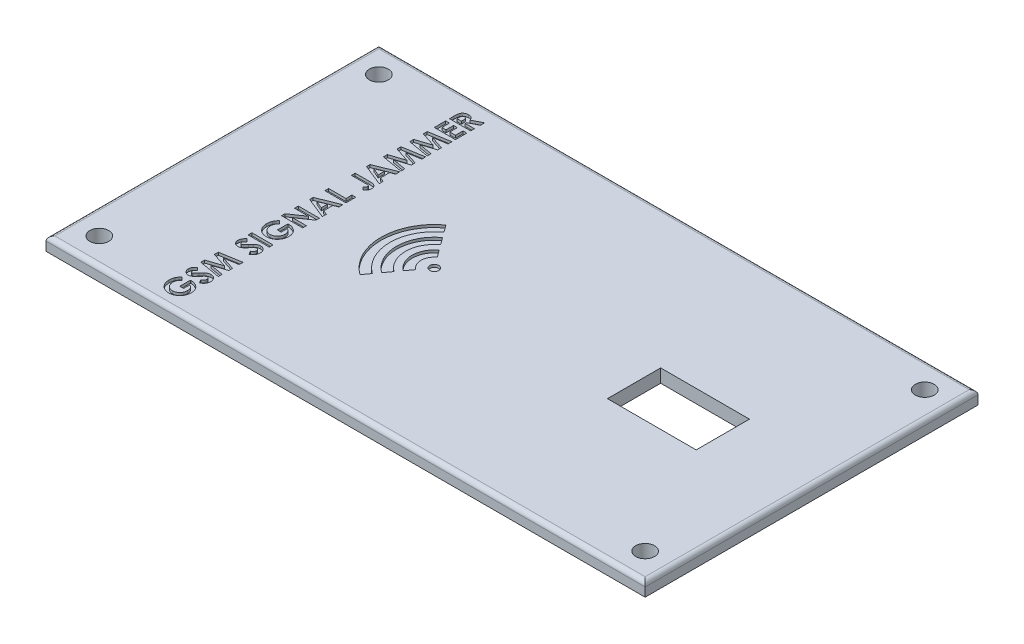
SolidWorks part; units mm, degrees
ref_plane "Front Plane" through (0, 0, 0) normal (0, 0, 1) x (1, 0, 0)
ref_plane "Top Plane" through (0, 0, 0) normal (0, 1, 0) x (1, 0, 0)
ref_plane "Right Plane" through (0, 0, 0) normal (1, 0, 0) x (0, 0, -1)
sketch "Sketch1" plane through (0, 0, 0) normal (0, 1, 0) x (1, 0, 0)
  line L1 (0, 0) -> (135, 0)
  line L2 (0, 0) -> (0, 75)
  line L3 (0, 75) -> (135, 75)
  line L4 (135, 0) -> (135, 75)
  point P5 (2.5, 72.5)
  point P6 (130, 72.5)
  point P7 (130, 2.5)
  point P8 (2.5, 2.5)
  dimension "D1" = 135
  dimension "D2" = 75
  dimension "D3" = 2.5
  dimension "D4" = 2.5
  dimension "D5" = 5
  dimension "D6" = 2.5
extrude "Boss-Extrude1" add sketch "Sketch1" along normal blind 3
sketch "Sketch2" plane through (0, 3, 0) normal (0, 1, 0) x (1, 0, 0)
  line L0 (0, 75) -> (135, 75) construction
  line L1 (95, 43.5) -> (115, 43.5)
  line L2 (95, 43.5) -> (95, 31.5)
  line L3 (95, 31.5) -> (115, 31.5)
  line L4 (115, 43.5) -> (115, 31.5)
  line L5 (135, 0) -> (135, 75) construction
  dimension "D1" = 20
  dimension "D2" = 12
  dimension "D3" = 31.5
  dimension "D4" = 20
extrude "Cut-Extrude1" cut sketch "Sketch2" against normal blind 3
sketch "Sketch6" plane through (0, 3, 0) normal (0, 1, 0) x (1, 0, 0)
  line L0 (115, 37.5) -> (0, 37.5) construction
  line L1 (115, 31.5) -> (115, 43.5) construction
  line L2 (0, 75) -> (0, 0) construction
sketch "Sketch7" plane through (0, 3, 0) normal (0, 1, 0) x (1, 0, 0)
  line L0 (27.3432, 0) -> (27.3432, 75) construction
  line L1 (0, 0) -> (135, 0) construction
  line L2 (135, 75) -> (0, 75) construction
  text T0 "<b>GSM SIGNAL JAMMER</b>" font "Century Gothic" height in points 18
extrude "Cut-Extrude2" cut sketch "Sketch7" against normal blind 0.6
sketch "Sketch8" plane through (0, 3, 0) normal (0, 1, 0) x (1, 0, 0)
  line L0 (115, 37.5) -> (0, 37.5) construction
  line L1 (48.2299, 35.0779) -> (47.0498, 33.4631)
  line L2 (47, 37.5) -> (0, 37.5) construction
  line L3 (48.2299, 39.9221) -> (47.0498, 41.5369)
  line L4 (44.0996, 45.5738) -> (42.9196, 47.1885)
  line L5 (46.1648, 42.7479) -> (44.9847, 44.3627)
  line L6 (46.1648, 32.2521) -> (44.9847, 30.6373)
  line L7 (44.0996, 29.4262) -> (42.9196, 27.8115)
  arc A0 (48.2299, 39.9221) -> (48.2299, 35.0779) centre (50, 37.5) ccw
  arc A1 (47.0498, 41.5369) -> (47.0498, 33.4631) centre (50, 37.5) ccw
  arc A2 (46.1648, 42.7479) -> (46.1648, 32.2521) centre (50, 37.5) ccw
  arc A3 (44.9847, 44.3627) -> (44.9847, 30.6373) centre (50, 37.5) ccw
  arc A4 (44.0996, 45.5738) -> (44.0996, 29.4262) centre (50, 37.5) ccw
  arc A5 (42.9196, 47.1885) -> (42.9196, 27.8115) centre (50, 37.5) ccw
  circle A6 centre (50, 37.5) radius 1
  dimension "D2" = 6.5
  dimension "D4" = 10
  dimension "D6" = 2
  dimension "D8" = 3
  dimension "D9" = 2
  dimension "D1" = 5
  dimension "D3" = 8.5
  dimension "D5" = 12
  dimension "D7" = 50
  dimension "D11" = 4.8443
extrude "Cut-Extrude3" cut sketch "Sketch8" against normal blind 0.6
sketch "Sketch11" plane through (0, 3, 0) normal (0, 1, 0) x (1, 0, 0)
  line L0 (0, 75) -> (0, 0) construction
  line L1 (135, 75) -> (0, 75) construction
  line L2 (0, 0) -> (135, 0) construction
  line L3 (135, 0) -> (135, 75) construction
  point P0 (6, 69)
  point P1 (129, 69)
  point P2 (6, 6)
  point P3 (129, 6)
  dimension "D1" = 6
  dimension "D2" = 6
  dimension "D3" = 6
  dimension "D4" = 6
  dimension "D5" = 6
hole_wizard "Ø4.0mm Dowel Hole1" positions "Sketch12" profile "Sketch13" hole size "Ø4.0" standard "ANSI Metric"
sketch "Sketch12" plane through (0, 3, 0) normal (0, 1, 0) x (1, 0, 0)
  point P0 (6, 69)
  point P3 (6, 6)
  point P6 (129, 6)
  point P9 (129, 69)
sketch "Sketch13" plane through (6, 3, -69) normal (1, 0, 0) x (0, 0, 1)
  line L0 (0, 0) -> (0, 8.8)
  line L1 (0, 8.8) -> (2.125, 7.5232)
  line L2 (2.125, 7.5232) -> (2.125, 0)
  line L5 (2.125, 0) -> (0, 0)
  line L10 (0, 8.8) -> (-2.125, 7.5232) construction
  line L11 (0, -6.35) -> (0, 107.95) construction
  dimension "Hole Dia." = 4.25
  dimension "Hole Depth" = 8.8
  dimension "Drill Angle" = 118
fillet "Fillet1" radius 1 4 edges at (135, 3, -37.5) (67.5, 3, 0) (67.5, 3, -75) (0, 3, -37.5)
